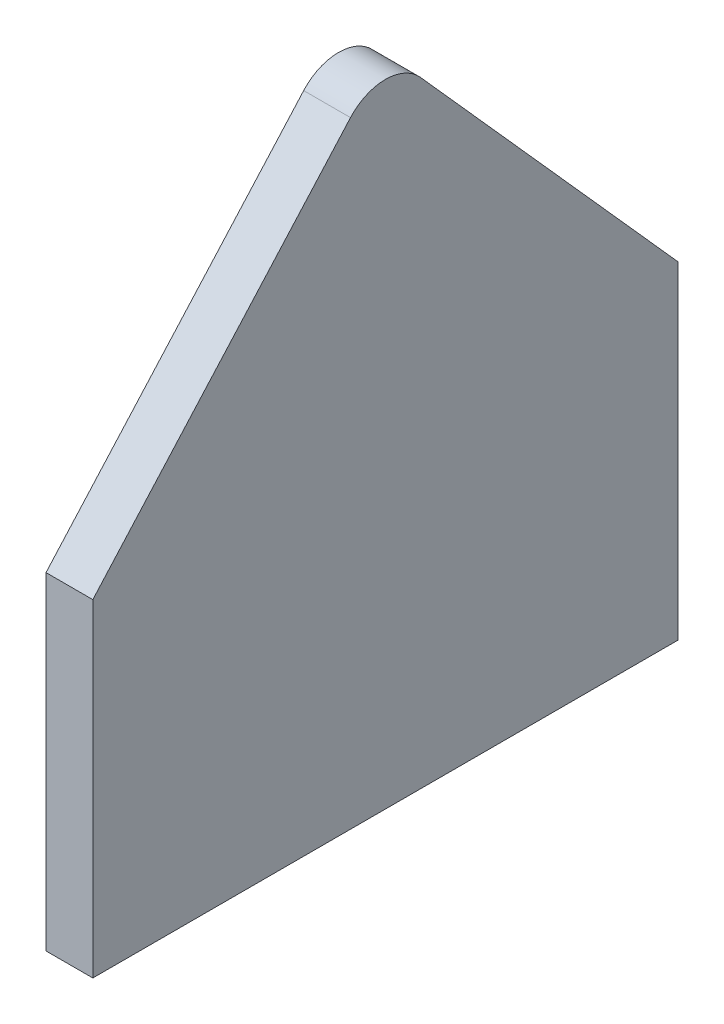
SolidWorks part; units mm, degrees
ref_plane "Front Plane" through (0, 0, 0) normal (0, 0, 1) x (1, 0, 0)
ref_plane "Top Plane" through (0, 0, 0) normal (0, 1, 0) x (1, 0, 0)
ref_plane "Right Plane" through (0, 0, 0) normal (1, 0, 0) x (0, 0, -1)
sketch "Sketch1" plane through (0, 0, 0) normal (1, 0, 0) x (0, 0, -1)
  line L0 (0, 0) -> (0, 65.4315) construction
  line L1 (12.5, 0) -> (-12.5, 0)
  line L2 (-12.5, 0) -> (-12.5, 14)
  line L3 (-12.5, 14) -> (0, 28)
  line L4 (12.5, 0) -> (12.5, 14)
  line L5 (12.5, 14) -> (0, 28)
  dimension "D1" = 25
  dimension "D2" = 14
  dimension "D3" = 14
extrude "Boss-Extrude1" add sketch "Sketch1" along normal blind 2
fillet "Fillet1" radius 2 1 edges at (1, 28, 0)
